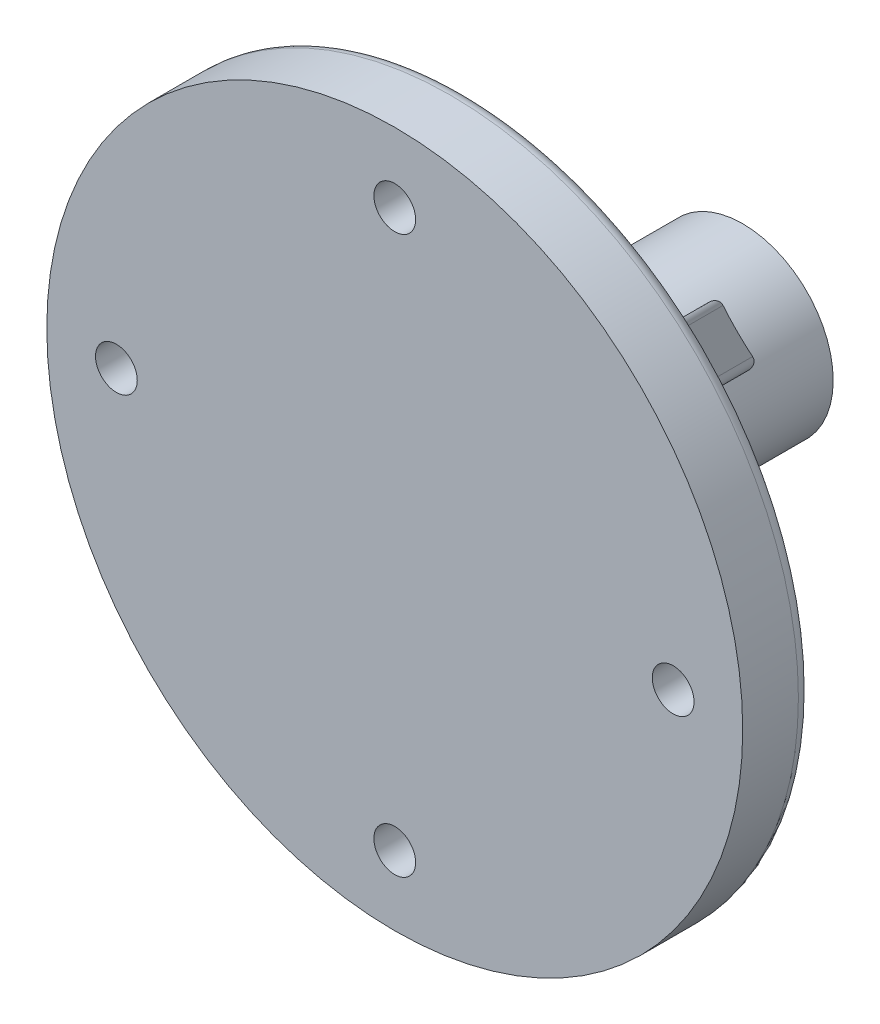
SolidWorks part; units mm, degrees
ref_plane "Спереди" through (0, 0, 0) normal (0, 0, 1) x (1, 0, 0)
ref_plane "Сверху" through (0, 0, 0) normal (0, 1, 0) x (1, 0, 0)
ref_plane "Справа" through (0, 0, 0) normal (1, 0, 0) x (0, 0, -1)
other "Configuration Table"
sketch "Sketch1" plane through (0, 0, 0) normal (0, 0, 1) x (1, 0, 0)
  circle A0 centre (0, 0) radius 6.5
  dimension "D1" = 13
extrude "Boss-Extrude1" add sketch "Sketch1" along normal blind 20 contours A0
sketch "Sketch4" plane through (0, 0, 0) normal (0, 0, -1) x (-1, 0, 0)
  circle A0 centre (0, 0) radius 2.6
  dimension "D1" = 5.2
extrude "Cut-Extrude1" cut sketch "Sketch4" against normal blind 15.5
fillet "Fillet1" radius 1 1 edges at (-2.6, 0, 15.5)
sketch "Sketch5" plane through (0, 0, 20) normal (0, 0, 1) x (1, 0, 0)
  circle A0 centre (0, 0) radius 25
  dimension "D1" = 50
extrude "Boss-Extrude2" add sketch "Sketch5" along normal blind 5
sketch "Sketch6" plane through (0, 0, 20) normal (0, 0, -1) x (-1, 0, 0)
  line L0 (-25, 0) -> (25, 0) construction
  line L1 (0, 25) -> (0, -25) construction
  line L2 (-17.6777, -17.6777) -> (17.6777, 17.6777) construction
  line L3 (17.6777, -17.6777) -> (-17.6777, 17.6777) construction
  circle A0 centre (0, 0) radius 25 construction
  circle A1 centre (0, 20) radius 1.5
  circle A2 centre (0, -20) radius 1.5
  circle A3 centre (-20, 0) radius 1.5
  circle A4 centre (20, 0) radius 1.5
  dimension "D3" = 3
  dimension "D1" = 45
  dimension "D2" = 45
  dimension "D4" = 40
  dimension "D5" = 40
extrude "Cut-Extrude2" cut sketch "Sketch6" against normal up to next
fillet "Fillet2" radius 7 1 edges at (6.5, 0, 20)
ref_plane "Plane1" through (0, 0, 0) normal (-0.7071, 0.7071, 0) x (0.7071, 0.7071, 0)
sketch "Sketch12" plane through (0, 0, 0) normal (-0.7071, 0.7071, 0) x (0.7071, 0.7071, 0)
  line L0 (6.5, -5) -> (21.5, -20)
  line L1 (6.5, -13) -> (6.5, 0) construction
  line L2 (25, -20) -> (-25, -20) construction
  dimension "D1" = 15
  dimension "D2" = 15
rib "Rib10" sketch "Sketch12" sketch "Sketch12" thickness 4 extrusion direction parallel to sketch draft on no parameters "D1"=4
pattern_circular "CirPattern1" count 4 over 360 about axis through (0, 0, 0) along (0, 0, 1) of "Rib10"
fillet "Fillet3" radius 1 1 edges at (25, 0, 20)
fillet "Fillet4" radius 0.5 8 edges at (8.3738, -11.2022, 12.3423) (11.2022, -8.3738, 12.3423) (-8.3738, -11.2022, 12.3423) (-11.2022, -8.3738, 12.3423) (11.2022, 8.3738, 12.3423) (8.3738, 11.2022, 12.3423) (-11.2022, 8.3738, 12.3423) (-8.3738, 11.2022, 12.3423)
sketch "Sketch13" plane through (0, 0, 20) normal (0, 0, -1) x (-1, 0, 0)
  circle A0 centre (-20, 0) radius 3
  circle A1 centre (0, 20) radius 3
  circle A2 centre (20, 0) radius 3
  circle A3 centre (0, -20) radius 3
  dimension "D1" = 6
extrude "Cut-Extrude3" cut sketch "Sketch13" against normal blind 1
